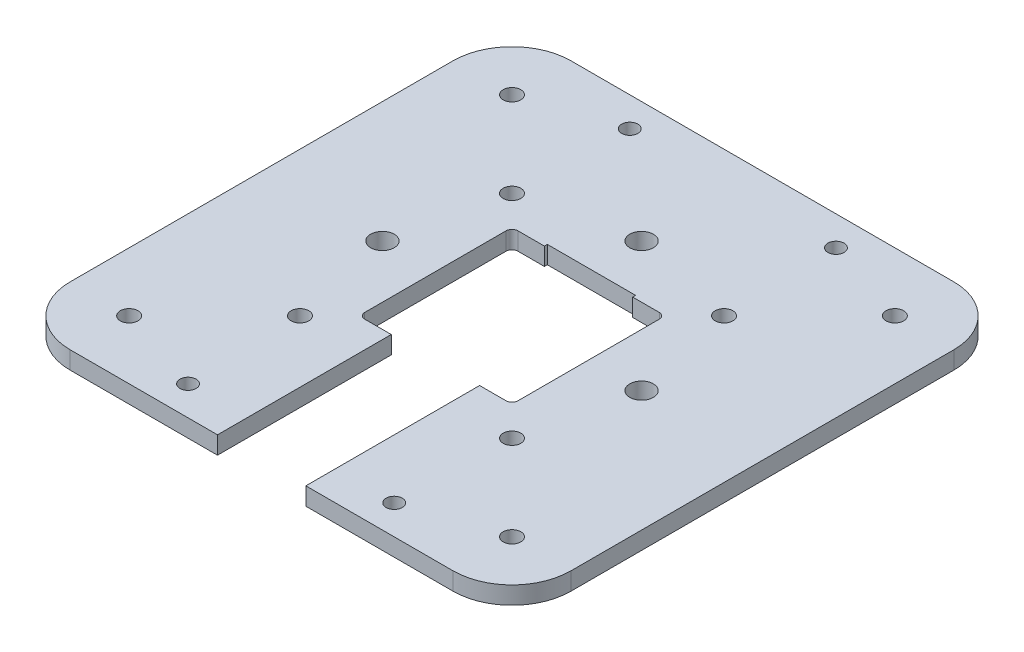
SolidWorks part; units mm, degrees
material "Acrylic (Medium-high impact)"
ref_plane "Front Plane" through (0, 0, 0) normal (0, 0, 1) x (1, 0, 0)
ref_plane "Top Plane" through (0, 0, 0) normal (0, 1, 0) x (1, 0, 0)
ref_plane "Right Plane" through (0, 0, 0) normal (1, 0, 0) x (0, 0, -1)
sketch "Sketch1" plane through (0, 0, 0) normal (0, 1, 0) x (1, 0, 0)
  line L0 (42.5, 25) -> (62.5, 25) construction
  line L1 (-42.5, -42.5) -> (42.5, -42.5)
  line L2 (-42.5, -42.5) -> (-42.5, 42.5)
  line L3 (-42.5, 42.5) -> (42.5, 42.5)
  line L4 (42.5, -42.5) -> (42.5, -25)
  line L5 (-42.5, -42.5) -> (42.5, 42.5) construction
  line L6 (-42.5, 42.5) -> (42.5, -42.5) construction
  line L7 (62.5, 25) -> (62.5, -25) construction
  line L8 (62.5, -25) -> (42.5, -25) construction
  line L9 (0, 0) -> (62.5, 0) construction
  line L10 (42.5, 25) -> (42.5, 42.5)
  line L11 (42.5, 25) -> (42.5, -25)
  point P0 (0, 0)
  dimension "D1" = 85
  dimension "D2" = 50
  dimension "D3" = 20
extrude "Boss-Extrude1" add sketch "Sketch1" along normal blind 3
fillet "Fillet1" radius 10 4 edges at (-42.5, 1.5, 42.5) (42.5, 1.5, 42.5) (42.5, 1.5, -42.5) (-42.5, 1.5, -42.5)
sketch "Sketch2" plane through (0, 3, 0) normal (0, 1, 0) x (1, 0, 0)
  line L0 (0, 0) -> (-22, 0) construction
  circle A0 centre (-32.5, 32.5) radius 1.5
  circle A1 centre (32.5, 32.5) radius 1.5
  circle A2 centre (32.5, -32.5) radius 1.5
  circle A3 centre (-32.5, -32.5) radius 1.5
  circle A4 centre (-17.5, -37.5) radius 1.375
  circle A5 centre (17.5, -37.5) radius 1.375
  circle A6 centre (-18, 18) radius 1.5
  circle A7 centre (-17.5, 37.5) radius 1.375
  arc A8 (42.5, 32.5) -> (32.5, 42.5) centre (32.5, 32.5) ccw construction
  circle A9 centre (17.5, 37.5) radius 1.375
  circle A10 centre (18, 18) radius 1.5
  circle A11 centre (18, -18) radius 1.5
  circle A12 centre (-18, -18) radius 1.5
  circle A13 centre (-22, 0) radius 2
  circle A14 centre (0, 22) radius 2
  circle A15 centre (22, 0) radius 2
  circle A16 centre (0, -22) radius 2
  point P35 (0, 0)
  point P44 (0, 0)
  dimension "D1" = 3
  dimension "D2" = 18
  dimension "D4" = 3
  dimension "D6" = 4
  dimension "D3" = 18
  dimension "D5" = 22
  dimension "D7" = 4
extrude "Cut-Extrude1" cut sketch "Sketch2" against normal up to next
sketch "Sketch3" plane through (0, 0, 0) normal (0, -1, 0) x (1, 0, 0)
  line L0 (-32.5, 42.5) -> (32.5, 42.5) construction
  line L1 (7.5, -13.5) -> (-7.5, -13.5)
  line L2 (7.5, -13.5) -> (7.5, -13)
  line L3 (7.5, 42.5) -> (-7.5, 42.5)
  line L4 (-7.5, -13.5) -> (-7.5, -13)
  line L5 (7.5, -13.5) -> (-7.5, 42.5) construction
  line L6 (7.5, 42.5) -> (-7.5, -13.5) construction
  line L7 (0, 0) -> (0, 14.5) construction
  line L8 (7.5, 13) -> (13, 13)
  line L9 (-13, 13) -> (-7.5, 13)
  line L10 (-13, 13) -> (-13, -13)
  line L11 (-13, -13) -> (-7.5, -13)
  line L12 (13, 13) -> (13, -13)
  line L13 (-13, 13) -> (13, -13) construction
  line L14 (-13, -13) -> (13, 13) construction
  line L15 (7.5, 13) -> (7.5, 42.5)
  line L16 (7.5, -13) -> (13, -13)
  line L17 (-7.5, 13) -> (-7.5, 42.5)
  point P0 (0, 14.5)
  dimension "D1" = 56
  dimension "D2" = 15
  dimension "D3" = 26
extrude "Cut-Extrude2" cut sketch "Sketch3" against normal up to next
fillet "Fillet2" radius 1 4 edges at (13, 1.5, -13) (13, 1.5, 13) (-13, 1.5, 13) (-13, 1.5, -13)
